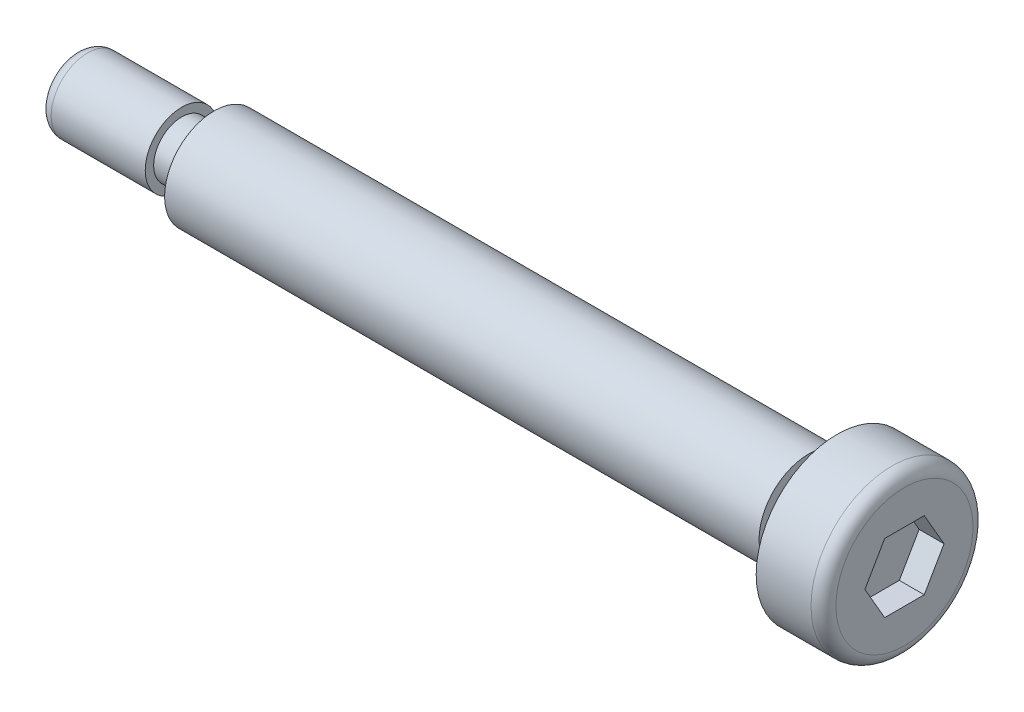
SolidWorks part; units mm, degrees
ref_plane "Front" through (0, 0, 0) normal (0, 0, 1) x (1, 0, 0)
ref_plane "Top" through (0, 0, 0) normal (0, 1, 0) x (1, 0, 0)
ref_plane "Right" through (0, 0, 0) normal (1, 0, 0) x (0, 0, -1)
sketch "Sketch2" plane through (0, 0, 0) normal (0, 0, 1) x (1, 0, 0)
  line L0 (-50, 3.97) -> (-2.3, 3.97)
  line L1 (-2.3, 3.97) -> (-2.3, 3.25)
  line L2 (-2.3, 3.25) -> (0, 3.25)
  line L3 (0, 3.25) -> (0, 6.5)
  line L4 (0, 6.5) -> (4.4, 6.5)
  line L5 (5.4, 5.5) -> (5.4, 0)
  line L6 (-50, 3.97) -> (-50, 2.25)
  line L7 (-50, 2.25) -> (-52.6, 2.25)
  line L8 (-52.6, 2.25) -> (-52.6, 2.925)
  line L9 (-52.6, 2.925) -> (-60.15, 2.925)
  line L10 (-61.15, 1.925) -> (-61.15, 0)
  line L11 (-61.15, 0) -> (5.4, 0) construction
  line L12 (5.4, 0) -> (-61.15, 0)
  arc A0 (-60.15, 2.925) -> (-61.15, 1.925) centre (-60.15, 1.925) ccw
  arc A1 (4.4, 6.5) -> (5.4, 5.5) centre (4.4, 5.5) cw
  point P19 (5.4, 6.5)
  dimension "D11" = 1
  dimension "D1" = 13
  dimension "D2" = 7.94
  dimension "D3" = 4.5
  dimension "D4" = 5.85
  dimension "D5" = 5.4
  dimension "D6" = 2.3
  dimension "D7" = 50
  dimension "D8" = 2.6
  dimension "D9" = 11.15
  dimension "D10" = 6.5
revolve "Revolve1" add sketch "Sketch2" angle 360 about L11
sketch "Sketch3" plane through (5.4, 0, 0) normal (1, 0, 0) x (0, 0, -1)
  line L1 (1.5877, 2.75) -> (-1.5877, 2.75)
  line L2 (-1.5877, 2.75) -> (-3.1754, 0)
  line L3 (-3.1754, 0) -> (-1.5877, -2.75)
  line L4 (-1.5877, -2.75) -> (1.5877, -2.75)
  line L5 (1.5877, -2.75) -> (3.1754, 0)
  line L6 (3.1754, 0) -> (1.5877, 2.75)
  circle A0 centre (0, 0) radius 2.75 construction
  dimension "D1" = 5.5
extrude "Cut-Extrude1" cut sketch "Sketch3" against normal blind 2
sketch "Sketch4" plane through (0, 0, 0) normal (0, 0, 1) x (1, 0, 0)
  circle A0 centre (-17.5, 0) radius 1.5
  dimension "D1" = 3
  dimension "D2" = 17.5
extrude "Cut-Extrude2" [suppressed] cut sketch "Sketch4" against normal through all both and the other way through all
sketch "Sketch5" plane through (0, 0, 0) normal (0, 0, 1) x (1, 0, 0)
  line L0 (-27.875, 0) -> (-27.875, 20.7854) construction
  line L1 (5.4, 0) -> (-61.15, 0)
  line L2 (-61.15, 1.925) -> (-61.15, -1.925) construction
  line L3 (-5.75, 0) -> (-5.75, 13.981)
  line L5 (-50, 0) -> (-50, 13.981)
  line L7 (-50, 3.97) -> (-50, -3.97) construction
ref_plane "Plane1" through (-27.875, 0, 0) normal (1, 0, 0) x (0, 0, -1)
